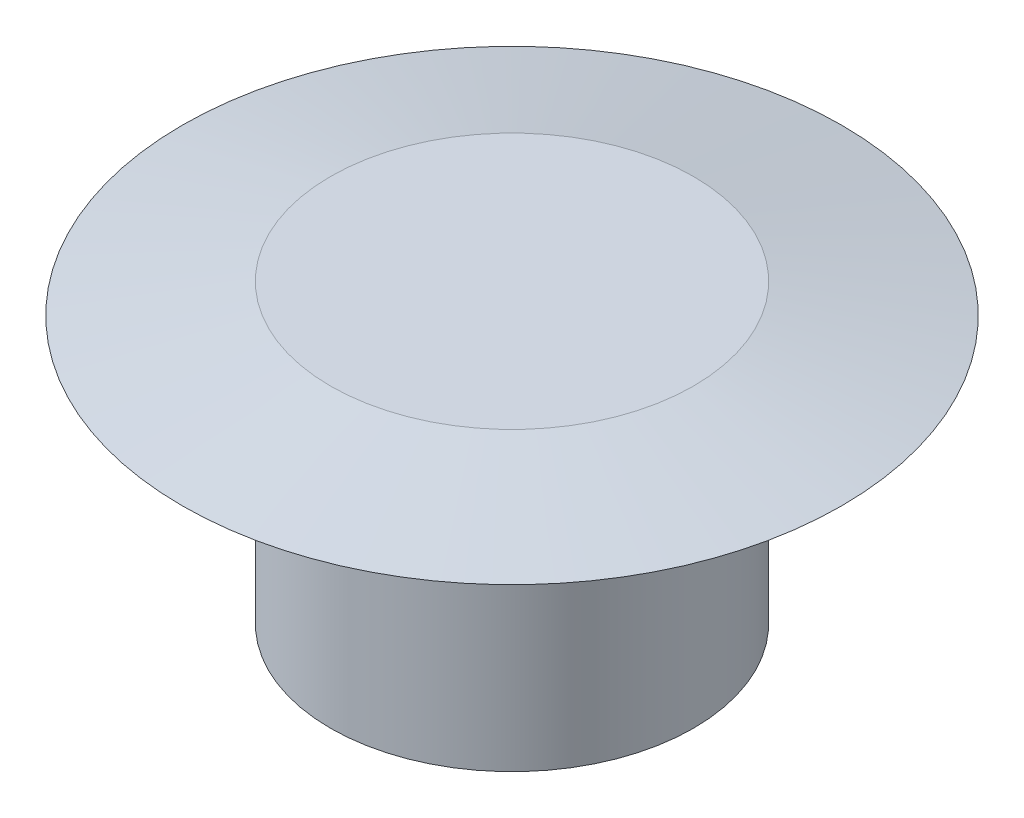
SolidWorks part; units mm, degrees
ref_plane "Alzado" through (0, 0, 0) normal (0, 0, 1) x (1, 0, 0)
ref_plane "Planta" through (0, 0, 0) normal (0, 1, 0) x (1, 0, 0)
ref_plane "Vista lateral" through (0, 0, 0) normal (1, 0, 0) x (0, 0, -1)
sketch "Croquis1" plane through (0, 0, 0) normal (0, 0, 1) x (1, 0, 0)
  line L0 (0, 0) -> (0, 16.2) construction
  line L1 (-10.9, 20) -> (-10.9, 0)
  line L2 (-10.9, 0) -> (-12.25, 0)
  line L3 (-12.25, 0) -> (-12.25, 18)
  line L4 (-12.25, 18) -> (-22.25, 18)
  line L5 (-22.25, 18) -> (-12.25, 20)
  line L6 (-12.25, 20) -> (-10.9, 20)
  point P7 (-12.25, 16.1339)
  dimension "D1" = 1.35
  dimension "D2" = 2
  dimension "D3" = 12.25
  dimension "D4" = 10
  dimension "D5" = 20
revolve "Revolución1" add sketch "Croquis1" angle 360 about L0
sketch "Croquis4" plane through (0, 20, 0) normal (0, 1, 0) x (1, 0, 0)
  circle A0 centre (0, 0) radius 10.9
extrude "Saliente-Extruir3" add sketch "Croquis4" against normal blind 1.35
